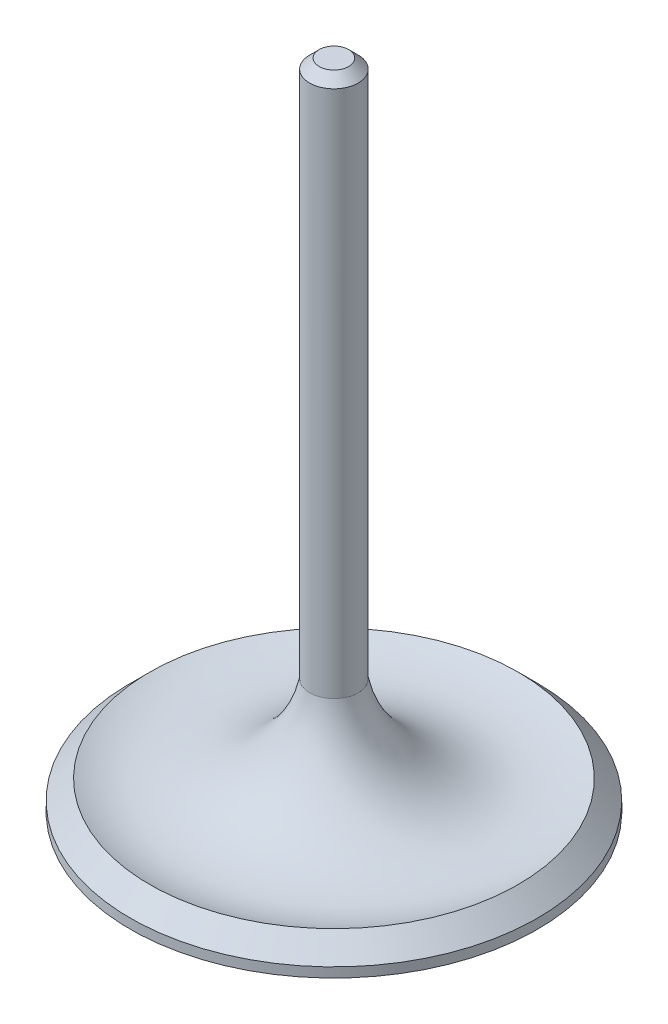
SolidWorks part; units mm, degrees
ref_plane "Front Plane" through (0, 0, 0) normal (0, 0, 1) x (1, 0, 0)
ref_plane "Top Plane" through (0, 0, 0) normal (0, 1, 0) x (1, 0, 0)
ref_plane "Right Plane" through (0, 0, 0) normal (1, 0, 0) x (0, 0, -1)
sketch "Sketch1" plane through (0, 0, 0) normal (1, 0, 0) x (0, 0, -1)
  line L0 (0, 0) -> (0, 85.55)
  line L1 (0, 85.55) -> (3.18, 85.55)
  line L2 (3.18, 85.55) -> (3.18, 15.1)
  line L3 (24.13, 3.81) -> (26.67, 1.27)
  line L4 (26.67, 1.27) -> (26.67, 0)
  line L5 (26.67, 0) -> (0, 0)
  arc A0 (3.18, 15.1) -> (24.13, 3.81) centre (18.1798, 17.8513) ccw
  point P8 (11.0353, 13.8079)
  dimension "D7" = 15.25
  dimension "D1" = 85.55
  dimension "D2" = 26.67
  dimension "D3" = 3.18
  dimension "D4" = 1.27
  dimension "D5" = 3.81
  dimension "D6" = 45
revolve "Revolve1" add sketch "Sketch1" angle 360 about L0
chamfer "Chamfer1" distance 1.25 angle 45 1 edges at (0, 85.55, -3.18)
